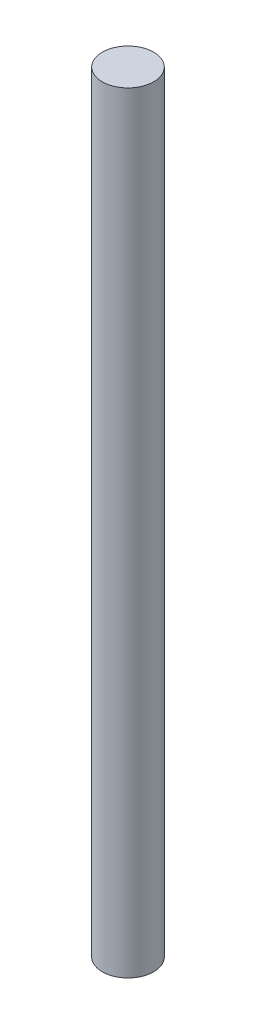
SolidWorks part; units mm, degrees
ref_plane "前视基准面" through (0, 0, 0) normal (0, 0, 1) x (1, 0, 0)
ref_plane "上视基准面" through (0, 0, 0) normal (0, 1, 0) x (1, 0, 0)
ref_plane "右视基准面" through (0, 0, 0) normal (1, 0, 0) x (0, 0, -1)
sketch "草图1" plane through (0, 0, 0) normal (0, 1, 0) x (1, 0, 0)
  circle A0 centre (0, 0) radius 2.5
  dimension "D1" = 5
extrude "凸台-拉伸1" add sketch "草图1" along normal blind 75
